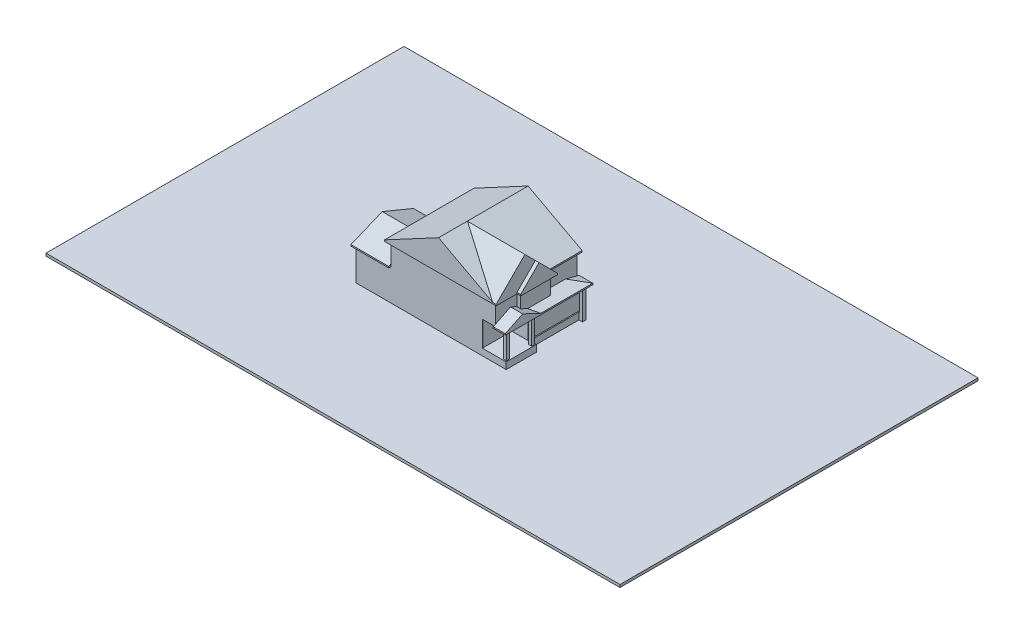
SolidWorks part; units mm, degrees
ref_plane "Front Plane" through (0, 0, 0) normal (0, 0, 1) x (1, 0, 0)
ref_plane "Top Plane" through (0, 0, 0) normal (0, 1, 0) x (1, 0, 0)
ref_plane "Right Plane" through (0, 0, 0) normal (1, 0, 0) x (0, 0, -1)
sketch "Sketch1" plane through (0, 0, 0) normal (0, 1, 0) x (1, 0, 0)
  line L0 (0, 0) -> (17208.5, 0)
  line L1 (0, 0) -> (0, 9448.8) construction
  line L2 (0, 0) -> (0, 6604)
  line L3 (0, 6604) -> (3048, 6604)
  line L4 (3048, 6604) -> (3048, 9448.8)
  line L5 (0, 9448.8) -> (17208.5, 9448.8) construction
  line L6 (3048, 9448.8) -> (16446.5, 9448.8)
  line L7 (16446.5, 9448.8) -> (16446.5, 0) construction
  line L8 (17208.5, 0) -> (17208.5, 3454.4)
  line L9 (17208.5, 9448.8) -> (17208.5, 0) construction
  line L10 (17208.5, 3454.4) -> (16446.5, 3454.4)
  line L11 (16446.5, 3454.4) -> (16446.5, 9093.2)
  line L12 (16446.5, 9093.2) -> (16852.9, 9093.2)
  line L13 (16852.9, 9093.2) -> (16852.9, 9448.8)
  line L14 (16852.9, 9448.8) -> (16446.5, 9448.8)
  line L15 (16852.9, 9448.8) -> (16852.9, 0) construction
extrude "Boss-Extrude1" add sketch "Sketch1" along normal blind 2603.5
ref_plane "Plane2" through (0, 2603.5, 0) normal (0, 1, 0) x (1, 0, 0)
sketch "Sketch2" plane through (0, 2603.5, 0) normal (0, 1, 0) x (1, 0, 0)
  line L11 (0, 0) -> (120.65, 0) construction
  line L12 (120.65, 127) -> (120.65, 6477)
  line L13 (120.65, 127) -> (14484.35, 127)
  line L14 (14484.35, 127) -> (14484.35, 3365.5)
  line L15 (14484.35, 3365.5) -> (16325.85, 3365.5)
  line L16 (120.65, 6477) -> (3168.65, 6477)
  line L17 (3168.65, 6477) -> (3168.65, 9328.15)
  line L18 (3168.65, 9328.15) -> (16325.85, 9328.15)
  line L19 (16325.85, 9328.15) -> (16325.85, 3365.5)
  line L20 (120.65, 127) -> (16325.85, 127) construction
  line L21 (0, 0) -> (17208.5, 0) construction
  line L22 (120.65, 0) -> (120.65, 127) construction
extrude "Boss-Extrude2" add sketch "Sketch2" along normal blind 3022.6
ref_plane "Plane3" through (0, 5626.1, 0) normal (0, 1, 0) x (1, 0, 0)
sketch "Sketch3" plane through (0, 5626.1, 0) normal (0, 1, 0) x (1, 0, 0)
  line L0 (16427.45, 9490.075) -> (4038.6, 9490.075) construction
  line L5 (4038.6, 9490.075) -> (15824.2, 9490.075)
  line L22 (4038.6, 9490.075) -> (4038.6, 53.975)
  line L23 (4038.6, 53.975) -> (16427.45, 53.975) construction
  line L24 (4038.6, 53.975) -> (16002, 53.975)
  line L25 (16427.45, 53.975) -> (16427.45, 9490.075) construction
  line L26 (16002, 53.975) -> (16002, 2435.225)
  line L27 (16002, 2435.225) -> (16427.45, 2435.225)
  line L28 (16427.45, 2435.225) -> (16427.45, 5832.475)
  line L29 (16427.45, 5832.475) -> (15824.2, 5832.475)
  line L30 (15824.2, 9490.075) -> (15824.2, 5832.475)
  point P6 (4038.6, 53.975)
extrude "Boss-Extrude3" add sketch "Sketch3" along normal blind 2463.8
ref_plane "Plane4" through (0, 1841.5, 0) normal (0, 1, 0) x (1, 0, 0)
sketch "Sketch4" plane through (0, 1841.5, 0) normal (0, 1, 0) x (1, 0, 0)
  line L10 (-20675.5654, 26188.1127) -> (45021.895, 26188.1127)
  line L11 (-20675.5654, 26188.1127) -> (-20675.5654, -14791.7177)
  line L12 (-20675.5654, -14791.7177) -> (45021.895, -14791.7177)
  line L13 (45021.895, 26188.1127) -> (45021.895, -14791.7177)
  line L14 (-20675.5654, 26188.1127) -> (45021.895, -14791.7177) construction
  line L15 (-20675.5654, -14791.7177) -> (45021.895, 26188.1127) construction
  point P0 (12173.1648, 5698.1975)
extrude "Boss-Extrude4" add sketch "Sketch4" against normal blind 304.8
sketch "Sketch5" plane through (0, 1536.7, 0) normal (0, -1, 0) x (1, 0, 0)
  line L1 (-2558.0149, -11208.2939) -> (19337.0017, -11208.2939)
  line L2 (-2558.0149, -11208.2939) -> (-2558.0149, 1114.2664)
  line L3 (-2558.0149, 1114.2664) -> (19337.0017, 1114.2664)
  line L4 (19337.0017, -11208.2939) -> (19337.0017, 1114.2664)
extrude "Cut-Extrude1" cut sketch "Sketch5" along normal blind 1905
ref_plane "Plane5" through (0, 8089.9, 0) normal (0, 1, 0) x (1, 0, 0)
ref_plane "Plane6" through (-285.75, 0, 0) normal (-1, 0, 0) x (0, 0, 1)
sketch "Sketch6" plane through (-285.75, 0, 0) normal (-1, 0, 0) x (0, 0, 1)
  line L0 (-127, 5626.1) -> (-6477, 5626.1)
  line L1 (-6477, 5626.1) -> (-6883.4, 5626.1)
  line L2 (2154.8725, 5626.1) -> (-2154.8725, 5626.1) construction
  line L3 (-127, 5626.1) -> (279.4, 5626.1)
  line L4 (-6883.4, 5626.1) -> (-3302, 7109.5645)
  line L5 (279.4, 5626.1) -> (-3302, 7109.5645)
extrude "Boss-Extrude5" add sketch "Sketch6" against normal up to surface (4324.35 mm away) up to face at (4038.6, 6447.3667, -4757.2083)
ref_plane "Plane8" through (0, 0, -9734.55) normal (0, 0, -1) x (-1, 0, 0)
sketch "Sketch8" plane through (0, 0, -9734.55) normal (0, 0, -1) x (-1, 0, 0)
  line L0 (-4038.6, 5626.1) -> (-3168.65, 5626.1)
  line L1 (-3168.65, 5626.1) -> (-2762.25, 5626.1)
  line L2 (-3168.65, 5626.1) -> (-120.65, 5626.1) construction
  line L3 (-2762.25, 5626.1) -> (-4038.6, 6154.7815)
  line L4 (-4038.6, 5626.1) -> (-4038.6, 6154.7815)
  line L5 (-4038.6, 7109.5645) -> (-4038.6, 5626.1) construction
extrude "Boss-Extrude6" add sketch "Sketch8" against normal up to surface (2851.15 mm away)
ref_plane "Plane9" through (2762.25, 0, 0) normal (-1, 0, 0) x (0, 0, 1)
sketch "Sketch9" plane through (2762.25, 0, 0) normal (-1, 0, 0) x (0, 0, 1)
  line L0 (-9734.55, 5626.1) -> (-8458.2, 6154.7815)
  line L1 (-9734.55, 5626.1) -> (-9734.55, 6154.7815)
  line L2 (-9734.55, 6154.7815) -> (-8458.2, 6154.7815)
extrude "Cut-Extrude2" cut sketch "Sketch9" against normal up to surface (1276.35 mm away) up to face at (4038.6, 6893.8526, -4666.1917)
ref_plane "Plane10" through (0, 0, -9896.475) normal (0, 0, -1) x (-1, 0, 0)
sketch "Sketch10" plane through (0, 0, -9896.475) normal (0, 0, -1) x (-1, 0, 0)
  line L0 (-4038.6, 8089.9) -> (-15824.2, 8089.9)
  line L1 (-15824.2, 8089.9) -> (-16230.6, 8089.9)
  line L2 (-4038.6, 8089.9) -> (-3632.2, 8089.9)
  line L3 (-3632.2, 8089.9) -> (-9931.4, 11456.8925)
  line L4 (-16230.6, 8089.9) -> (-9931.4, 11456.8925)
extrude "Boss-Extrude7" add sketch "Sketch10" against normal up to surface (9842.5 mm away) up to face at (8823.96, 6639.2377, -53.975)
sketch "Sketch11" plane through (0, 0, -53.975) normal (0, 0, 1) x (1, 0, 0)
  line L0 (3632.2, 8089.9) -> (9931.4, 11456.8925)
  line L1 (9931.4, 11456.8925) -> (16230.6, 8089.9)
  line L2 (16230.6, 8089.9) -> (3632.2, 8089.9)
extrude "Boss-Extrude8" add sketch "Sketch11" along normal blind 406.4
sketch "Sketch12" plane through (0, 0, 352.425) normal (0, 0, 1) x (1, 0, 0)
  line L0 (16002, 8089.9) -> (16230.6, 8089.9)
  line L1 (16230.6, 8089.9) -> (9931.4, 11456.8925)
  line L2 (16002, 8089.9) -> (9817.1, 11395.7979)
  line L3 (9931.4, 11456.8925) -> (9817.1, 11395.7979)
  line L4 (9931.4, 11456.8925) -> (3632.2, 8089.9) construction
extrude "Cut-Extrude3" cut sketch "Sketch12" against normal blind 11303
ref_plane "Plane11" through (16833.85, 0, 0) normal (1, 0, 0) x (0, 0, -1)
sketch "Sketch13" plane through (16833.85, 0, 0) normal (1, 0, 0) x (0, 0, -1)
  line L0 (5832.475, 8089.9) -> (2435.225, 8089.9)
  line L1 (2435.225, 8089.9) -> (2028.825, 8089.9)
  line L2 (53.975, 8089.9) -> (2435.225, 8089.9) construction
  line L3 (5832.475, 8089.9) -> (6238.875, 8089.9)
  line L4 (5832.475, 8089.9) -> (9490.075, 8089.9) construction
  line L5 (6238.875, 8089.9) -> (4133.85, 10194.925)
  line L6 (2028.825, 8089.9) -> (4133.85, 10194.925)
extrude "Boss-Extrude9" add sketch "Sketch13" against normal up to surface (831.85 mm away)
ref_plane "Plane12" through (16408.4, 0, 0) normal (1, 0, 0) x (0, 0, -1)
sketch "Sketch14" plane through (16408.4, 0, 0) normal (1, 0, 0) x (0, 0, -1)
  line L0 (-352.425, 8089.9) -> (2943.225, 11385.55)
  line L1 (4133.85, 10194.925) -> (2943.225, 11385.55)
  line L2 (-352.425, 8089.9) -> (2028.825, 8089.9)
  line L3 (2028.825, 8089.9) -> (4133.85, 10194.925)
extrude "Boss-Extrude10" add sketch "Sketch14" against normal up to surface (6572.1275 mm away)
sketch "Sketch15" plane through (0, 2603.5, 0) normal (0, 1, 0) x (1, 0, 0)
  line L0 (16852.9, 9093.2) -> (16446.5, 9093.2) construction
  line L1 (16852.9, 9448.8) -> (16497.3, 9448.8)
  line L2 (16852.9, 9448.8) -> (16852.9, 9093.2)
  line L3 (16852.9, 9093.2) -> (16497.3, 9093.2)
  line L4 (16497.3, 9448.8) -> (16497.3, 9093.2)
  line L5 (17208.5, 3454.4) -> (17106.9, 3454.4) construction
  line L6 (17208.5, 3454.4) -> (16446.5, 3454.4) construction
  line L7 (17106.9, 3454.4) -> (17106.9, 0) construction
  line L8 (17208.5, 0) -> (0, 0) construction
  line L9 (14599.9775, 126.9667) -> (17106.9, 126.9667) construction
  line L10 (14484.2237, 3365.4116) -> (17106.9, 3365.4116) construction
  line L11 (17106.9, 3009.8116) -> (16751.3, 3009.8116)
  line L12 (17106.9, 3365.4116) -> (16778.8236, 3365.4116)
  line L13 (17106.9, 3365.4116) -> (17106.9, 3009.8116)
  line L16 (17106.9, 126.9667) -> (16751.3, 126.9667)
  line L17 (17106.9, 126.9667) -> (17106.9, 482.5667)
  line L18 (17106.9, 482.5667) -> (16751.3, 482.5667)
  line L19 (16751.3, 126.9667) -> (16751.3, 482.5667)
  line L20 (16751.3, 3009.8116) -> (16751.3, 3365.4116)
  line L21 (16751.3, 3365.4116) -> (16778.8236, 3365.4116)
extrude "Boss-Extrude11" add sketch "Sketch15" along normal blind 3022.6
ref_plane "Plane13" through (0, 0, -9728.2) normal (0, 0, -1) x (-1, 0, 0)
sketch "Sketch16" plane through (0, 0, -9728.2) normal (0, 0, -1) x (-1, 0, 0)
  line L0 (-15824.2, 5626.1) -> (-17106.9, 5626.1)
  line L1 (-17106.9, 5626.1) -> (-17386.3, 5626.1)
  line L2 (-17386.3, 5626.1) -> (-15824.2, 6044.6634)
  line L3 (-15824.2, 5626.1) -> (-15824.2, 6044.6634)
extrude "Boss-Extrude12" add sketch "Sketch16" against normal blind 7362.952
ref_plane "Plane14" through (17132.3, 0, 0) normal (1, 0, 0) x (0, 0, -1)
sketch "Sketch17" plane through (17132.3, 0, 0) normal (1, 0, 0) x (0, 0, -1)
  line L0 (9734.55, 5626.1) -> (8172.45, 6044.6634)
  line L1 (9734.55, 5626.1) -> (9728.2, 6044.6634)
  line L2 (9728.2, 6044.6634) -> (8172.45, 6044.6634)
extrude "Cut-Extrude4" cut sketch "Sketch17" against normal up to surface (1308.1 mm away) and the other way blind 304.8 up to face at (15824.2, 7067.2817, -7661.275)
sketch "Sketch18" plane through (17132.3, 0, 0) normal (1, 0, 0) x (0, 0, -1)
  line L0 (-279.4, 5626.1) -> (1704.3334, 6604.369)
  line L1 (-279.4, 5626.1) -> (126.9667, 5626.1)
  line L2 (126.9667, 5626.1) -> (3365.4116, 5626.1)
  line L3 (3365.4116, 5626.1) -> (3771.8116, 5626.1)
  line L4 (2365.248, 5626.1) -> (9728.2, 5626.1) construction
  line L5 (3771.8116, 5626.1) -> (1704.3334, 6604.369)
extrude "Boss-Extrude13" add sketch "Sketch18" against normal up to surface and the other way blind 254 up to face at (16002, 6571.0074, -1618.1493)
sketch "Sketch19" plane through (0, 2603.5, 0) normal (0, 1, 0) x (1, 0, 0)
  line L1 (0, 0) -> (14484.5023, 0)
  line L2 (0, 0) -> (0, 133.0525)
  line L3 (0, 133.0525) -> (14484.5023, 133.0525)
  line L4 (14484.5023, 0) -> (14484.5023, 133.0525)
extrude "Boss-Extrude14" add sketch "Sketch19" along normal blind 3022.6
sketch "Sketch20" plane through (0, 5626.1, 0) normal (0, 1, 0) x (1, 0, 0)
  line L0 (17208.5, 0) -> (0, 0) construction
  line L1 (4038.6, 0) -> (14484.5023, 0)
  line L2 (4038.6, 0) -> (4038.6, 57.769)
  line L3 (4038.6, 57.769) -> (14484.5023, 57.769)
  line L4 (14484.5023, 0) -> (14484.5023, 57.769)
  line L5 (4038.6, 0) -> (14484.5023, 0) construction
  line L6 (14484.5023, 0) -> (14484.5023, 133.0525) construction
extrude "Boss-Extrude15" add sketch "Sketch20" along normal blind 2601.214
sketch "Sketch22" plane through (14484.5023, 0, 0) normal (1, 0, 0) x (0, 0, -1)
  line L1 (53.975, 5626.1) -> (0, 5626.1)
  line L2 (53.975, 5626.1) -> (53.975, 8089.9)
  line L3 (53.975, 8089.9) -> (0, 8089.9)
  line L4 (0, 5626.1) -> (0, 8089.9)
extrude "Boss-Extrude17" add sketch "Sketch22" along normal up to surface (1517.4977 mm away) up to face at (16002, 6966.6409, -1336.5467)
sketch "Sketch23" plane through (0, 2603.5, 0) normal (0, 1, 0) x (1, 0, 0)
  line L0 (0, 6604) -> (0, 133.0525)
  line L1 (120.65, 133.0525) -> (0, 133.0525)
  line L2 (120.65, 133.0525) -> (120.65, 6477)
  line L7 (3048, 6604) -> (0, 6604)
  line L9 (3048, 9448.8) -> (3168.65, 9448.8)
  line L10 (3048, 9448.8) -> (3048, 6604)
  line L12 (3168.65, 9328.15) -> (3168.65, 6477)
  line L13 (3168.65, 6477) -> (120.65, 6477)
  line L14 (3168.65, 9448.8) -> (16497.3, 9448.8)
  line L15 (16497.3, 9448.8) -> (16497.3, 9328.15)
  line L16 (16497.3, 9448.8) -> (16497.3, 9093.2) construction
  line L17 (16497.3, 9328.15) -> (3168.65, 9328.15)
extrude "Boss-Extrude18" add sketch "Sketch23" along normal blind 3022.6
sketch "Sketch24" plane through (0, 5626.1, 0) normal (0, -1, 0) x (1, 0, 0)
  line L1 (16852.9, -9448.8) -> (4038.6, -9448.8)
  line L2 (16852.9, -9448.8) -> (16852.9, -9490.075)
  line L3 (16852.9, -9490.075) -> (4038.6, -9490.075)
  line L5 (3048, -9448.8) -> (4038.6, -9448.8)
  line L6 (3048, -9448.8) -> (3048, -9490.075)
  line L7 (3048, -9490.075) -> (4038.6, -9490.075)
extrude "Boss-Extrude19" add sketch "Sketch24" along normal up to surface (3784.6 mm away) up to face at (12173.1648, 1841.5, -5698.1975)
sketch "Sketch25" plane through (0, 8089.9, 0) normal (0, -1, 0) x (1, 0, 0)
  line L45 (4140.2, -155.575) -> (4140.2, -9388.475)
  line L46 (4140.2, -9388.475) -> (15494, -9388.475)
  line L47 (15494, -9388.475) -> (15494, -5730.875)
  line L48 (15494, -5730.875) -> (16325.85, -5730.875)
  line L49 (16325.85, -5730.875) -> (16325.85, -2536.825)
  line L50 (16325.85, -2536.825) -> (15900.4, -2536.825)
  line L51 (15900.4, -2536.825) -> (15900.4, -155.575)
  line L52 (15900.4, -155.575) -> (15900.4, -155.575)
  line L53 (15900.4, -155.575) -> (4140.2, -155.575)
  line L54 (3632.2, 352.425) -> (3632.2, -9896.475)
  line L55 (16408.4, 352.425) -> (16002, 352.425)
  line L56 (16002, 352.425) -> (3632.2, 352.425)
  line L57 (16408.4, -2028.825) -> (16408.4, 352.425)
  line L58 (16833.85, -2028.825) -> (16408.4, -2028.825)
  line L59 (16833.85, -6238.875) -> (16833.85, -2028.825)
  line L60 (16002, -6238.875) -> (16833.85, -6238.875)
  line L61 (16002, -9896.475) -> (16002, -6238.875)
  line L62 (3632.2, -9896.475) -> (16002, -9896.475)
  line L63 (3632.2, 352.425) -> (3632.2, -9896.475)
  line L64 (16408.4, 352.425) -> (16002, 352.425)
  line L65 (16002, 352.425) -> (3632.2, 352.425)
  line L66 (16408.4, -2028.825) -> (16408.4, 352.425)
  line L67 (16833.85, -2028.825) -> (16408.4, -2028.825)
  line L68 (16833.85, -6238.875) -> (16833.85, -2028.825)
  line L69 (16002, -6238.875) -> (16833.85, -6238.875)
  line L70 (16002, -9896.475) -> (16002, -6238.875)
  line L71 (3632.2, -9896.475) -> (16002, -9896.475)
  dimension "D1" = 0
  dimension "D2" = 508
extrude "Boss-Extrude20" add sketch "Sketch25" along normal blind 152.4
sketch "Sketch26" plane through (0, 5626.1, 0) normal (0, -1, 0) x (1, 0, 0)
  line L120 (3530.6, -508) -> (3530.6, -228.6)
  line L121 (3530.6, -228.6) -> (222.25, -228.6)
  line L122 (222.25, -228.6) -> (222.25, -6375.4)
  line L123 (222.25, -6375.4) -> (3270.25, -6375.4)
  line L124 (3270.25, -6375.4) -> (3270.25, -9226.55)
  line L125 (3270.25, -9226.55) -> (3530.6, -9226.55)
  line L126 (3530.6, -9226.55) -> (3530.6, -8982.075)
  line L127 (3530.6, -8982.075) -> (16332.2, -8982.075)
  line L128 (16332.2, -8982.075) -> (16332.2, -9220.2)
  line L129 (16332.2, -9220.2) -> (16878.3, -9220.2)
  line L130 (16878.3, -9220.2) -> (16878.3, -3771.8116)
  line L131 (16878.3, -3771.8116) -> (16878.3, -228.6)
  line L132 (16878.3, -228.6) -> (16510, -228.6)
  line L133 (16510, -228.6) -> (16510, -508)
  line L134 (16510, -508) -> (3530.6, -508)
  line L135 (4038.6, 0) -> (4038.6, 279.4)
  line L136 (4038.6, 279.4) -> (-285.75, 279.4)
  line L137 (-285.75, 279.4) -> (-285.75, -6883.4)
  line L138 (-285.75, -6883.4) -> (2762.25, -6883.4)
  line L139 (2762.25, -6883.4) -> (2762.25, -9734.55)
  line L140 (2762.25, -9734.55) -> (4038.6, -9734.55)
  line L141 (4038.6, -9734.55) -> (4038.6, -9490.075)
  line L142 (4038.6, -9490.075) -> (15824.2, -9490.075)
  line L143 (15824.2, -9490.075) -> (15824.2, -9728.2)
  line L144 (15824.2, -9728.2) -> (17386.3, -9728.2)
  line L145 (17386.3, -9728.2) -> (17386.3, -3771.8116)
  line L146 (17386.3, -3771.8116) -> (17386.3, 279.4)
  line L147 (17386.3, 279.4) -> (16002, 279.4)
  line L148 (16002, 279.4) -> (16002, 0)
  line L149 (16002, 0) -> (4038.6, 0)
  line L150 (4038.6, 0) -> (4038.6, 279.4)
  line L151 (4038.6, 279.4) -> (-285.75, 279.4)
  line L152 (-285.75, 279.4) -> (-285.75, -6883.4)
  line L153 (-285.75, -6883.4) -> (2762.25, -6883.4)
  line L154 (2762.25, -6883.4) -> (2762.25, -9734.55)
  line L155 (2762.25, -9734.55) -> (4038.6, -9734.55)
  line L156 (4038.6, -9734.55) -> (4038.6, -9490.075)
  line L157 (4038.6, -9490.075) -> (15824.2, -9490.075)
  line L158 (15824.2, -9490.075) -> (15824.2, -9728.2)
  line L159 (15824.2, -9728.2) -> (17386.3, -9728.2)
  line L160 (17386.3, -9728.2) -> (17386.3, -3771.8116)
  line L161 (17386.3, -3771.8116) -> (17386.3, 279.4)
  line L162 (17386.3, 279.4) -> (16002, 279.4)
  line L163 (16002, 279.4) -> (16002, 0)
  line L164 (16002, 0) -> (4038.6, 0)
  dimension "D1" = 0
  dimension "D2" = 508
extrude "Boss-Extrude21" add sketch "Sketch26" along normal blind 152.4
sketch "Sketch27" plane through (0, 0, -9328.15) normal (0, 0, 1) x (1, 0, 0)
  line L0 (16497.3, 5473.7) -> (16497.3, 2603.5) construction
  line L1 (16325.85, 2603.5) -> (16497.3, 2603.5)
  line L2 (16325.85, 2603.5) -> (16325.85, 5473.7)
  line L3 (16325.85, 5473.7) -> (16497.3, 5473.7)
  line L4 (16497.3, 2603.5) -> (16497.3, 5473.7)
extrude "Cut-Extrude5" cut sketch "Sketch27" against normal blind 405.13
sketch "Truss Sketch 1" plane through (-2556.1241, 4782.1719, 0) normal (-0.4714, 0.8819, 0) x (0.8819, 0.4714, 0)
  line L0 (14029.8512, -352.425) -> (14029.8512, -314.325) construction
  line L1 (14029.8512, 9896.475) -> (14029.8512, -352.425) construction
  line L2 (14029.8512, -314.325) -> (7016.8669, -314.325) construction
  line L3 (7016.8669, -352.425) -> (7016.8669, 9896.475) construction
  line L4 (7016.8669, -314.325) -> (7016.8669, -352.425) construction
  line L5 (6945.026, -352.425) -> (7016.8669, -352.425) construction
  line L6 (7016.8669, -352.425) -> (14029.8512, -352.425) construction
  line L7 (14029.8512, 257.175) -> (14029.8512, 295.275) construction
  line L8 (14029.8512, 295.275) -> (7016.8669, 295.275) construction
  line L9 (7016.8669, 295.275) -> (7016.8669, 257.175) construction
  line L10 (7016.8669, 257.175) -> (14029.8512, 257.175) construction
  line L11 (14029.8512, 866.775) -> (14029.8512, 904.875) construction
  line L12 (14029.8512, 904.875) -> (7016.8669, 904.875) construction
  line L13 (7016.8669, 904.875) -> (7016.8669, 866.775) construction
  line L14 (7016.8669, 866.775) -> (14029.8512, 866.775) construction
  line L15 (14029.8512, 1476.375) -> (14029.8512, 1514.475) construction
  line L16 (14029.8512, 1514.475) -> (7016.8669, 1514.475) construction
  line L17 (7016.8669, 1514.475) -> (7016.8669, 1476.375) construction
  line L18 (7016.8669, 1476.375) -> (14029.8512, 1476.375) construction
  line L19 (14029.8512, 2085.975) -> (14029.8512, 2124.075) construction
  line L20 (14029.8512, 2124.075) -> (7016.8669, 2124.075) construction
  line L21 (7016.8669, 2124.075) -> (7016.8669, 2085.975) construction
  line L22 (7016.8669, 2085.975) -> (14029.8512, 2085.975) construction
  line L23 (14029.8512, 2695.575) -> (14029.8512, 2733.675) construction
  line L24 (14029.8512, 2733.675) -> (7016.8669, 2733.675) construction
  line L25 (7016.8669, 2733.675) -> (7016.8669, 2695.575) construction
  line L26 (7016.8669, 2695.575) -> (14029.8512, 2695.575) construction
  line L27 (14029.8512, 3305.175) -> (14029.8512, 3343.275) construction
  line L28 (14029.8512, 3343.275) -> (7016.8669, 3343.275) construction
  line L29 (7016.8669, 3343.275) -> (7016.8669, 3305.175) construction
  line L30 (7016.8669, 3305.175) -> (14029.8512, 3305.175) construction
  line L31 (14029.8512, 3914.775) -> (14029.8512, 3952.875) construction
  line L32 (14029.8512, 3952.875) -> (7016.8669, 3952.875) construction
  line L33 (7016.8669, 3952.875) -> (7016.8669, 3914.775) construction
  line L34 (7016.8669, 3914.775) -> (14029.8512, 3914.775) construction
  line L35 (14029.8512, 4524.375) -> (14029.8512, 4562.475) construction
  line L36 (14029.8512, 4562.475) -> (7016.8669, 4562.475) construction
  line L37 (7016.8669, 4562.475) -> (7016.8669, 4524.375) construction
  line L38 (7016.8669, 4524.375) -> (14029.8512, 4524.375) construction
  line L39 (14029.8512, 5133.975) -> (14029.8512, 5172.075) construction
  line L40 (14029.8512, 5172.075) -> (7016.8669, 5172.075) construction
  line L41 (7016.8669, 5172.075) -> (7016.8669, 5133.975) construction
  line L42 (7016.8669, 5133.975) -> (14029.8512, 5133.975) construction
  line L43 (14029.8512, 5743.575) -> (14029.8512, 5781.675) construction
  line L44 (14029.8512, 5781.675) -> (7016.8669, 5781.675) construction
  line L45 (7016.8669, 5781.675) -> (7016.8669, 5743.575) construction
  line L46 (7016.8669, 5743.575) -> (14029.8512, 5743.575) construction
  line L47 (14029.8512, 6353.175) -> (14029.8512, 6391.275) construction
  line L48 (14029.8512, 6391.275) -> (7016.8669, 6391.275) construction
  line L49 (7016.8669, 6391.275) -> (7016.8669, 6353.175) construction
  line L50 (7016.8669, 6353.175) -> (14029.8512, 6353.175) construction
  line L51 (14029.8512, 6962.775) -> (14029.8512, 7000.875) construction
  line L52 (14029.8512, 7000.875) -> (7016.8669, 7000.875) construction
  line L53 (7016.8669, 7000.875) -> (7016.8669, 6962.775) construction
  line L54 (7016.8669, 6962.775) -> (14029.8512, 6962.775) construction
  line L55 (14029.8512, 7572.375) -> (14029.8512, 7610.475) construction
  line L56 (14029.8512, 7610.475) -> (7016.8669, 7610.475) construction
  line L57 (7016.8669, 7610.475) -> (7016.8669, 7572.375) construction
  line L58 (7016.8669, 7572.375) -> (14029.8512, 7572.375) construction
  line L59 (14029.8512, 8181.975) -> (14029.8512, 8220.075) construction
  line L60 (14029.8512, 8220.075) -> (7016.8669, 8220.075) construction
  line L61 (7016.8669, 8220.075) -> (7016.8669, 8181.975) construction
  line L62 (7016.8669, 8181.975) -> (14029.8512, 8181.975) construction
  line L63 (14029.8512, 8791.575) -> (14029.8512, 8829.675) construction
  line L64 (14029.8512, 8829.675) -> (7016.8669, 8829.675) construction
  line L65 (7016.8669, 8829.675) -> (7016.8669, 8791.575) construction
  line L66 (7016.8669, 8791.575) -> (14029.8512, 8791.575) construction
  line L67 (14029.8512, 9401.175) -> (14029.8512, 9439.275) construction
  line L68 (14029.8512, 9439.275) -> (7016.8669, 9439.275) construction
  line L69 (7016.8669, 9439.275) -> (7016.8669, 9401.175) construction
  line L70 (7016.8669, 9401.175) -> (14029.8512, 9401.175) construction
  line L71 (14029.8512, 9896.475) -> (14029.8512, 9858.375) construction
  line L72 (14029.8512, 9858.375) -> (7016.8669, 9858.375) construction
  line L73 (7016.8669, 9858.375) -> (7016.8669, 9896.475) construction
  line L74 (7016.8669, 9896.475) -> (14029.8512, 9896.475) construction
  dimension "D1" = 17
sketch "Truss Sketch 2" plane through (0, 4900.9595, 2030.0439) normal (0, 0.9239, 0.3827) x (1, 0, 0)
  line L0 (4038.6, 5771.3627) -> (4038.6, 1894.8833) construction
  line L1 (4038.6, 1894.8833) -> (4000.5, 1894.8833) construction
  line L2 (4038.6, 1894.8833) -> (-285.75, 1894.8833) construction
  line L3 (4000.5, 1894.8833) -> (4000.5, 5771.3627) construction
  line L4 (4038.6, 5771.3627) -> (-285.75, 5771.3627) construction
  line L5 (4000.5, 5771.3627) -> (4038.6, 5771.3627) construction
  line L6 (-285.75, 1894.8833) -> (-285.75, 5771.3627) construction
  line L7 (-285.75, 5771.3627) -> (-247.65, 5771.3627) construction
  line L8 (-247.65, 5771.3627) -> (-247.65, 1894.8833) construction
  line L9 (-247.65, 1894.8833) -> (-285.75, 1894.8833) construction
  line L10 (323.85, 1894.8833) -> (323.85, 5771.3627) construction
  line L11 (323.85, 5771.3627) -> (361.95, 5771.3627) construction
  line L12 (361.95, 5771.3627) -> (361.95, 1894.8833) construction
  line L13 (361.95, 1894.8833) -> (323.85, 1894.8833) construction
  line L14 (933.45, 1894.8833) -> (933.45, 5771.3627) construction
  line L15 (933.45, 5771.3627) -> (971.55, 5771.3627) construction
  line L16 (971.55, 5771.3627) -> (971.55, 1894.8833) construction
  line L17 (971.55, 1894.8833) -> (933.45, 1894.8833) construction
  line L18 (1543.05, 1894.8833) -> (1543.05, 5771.3627) construction
  line L19 (1543.05, 5771.3627) -> (1581.15, 5771.3627) construction
  line L20 (1581.15, 5771.3627) -> (1581.15, 1894.8833) construction
  line L21 (1581.15, 1894.8833) -> (1543.05, 1894.8833) construction
  line L22 (2152.65, 1894.8833) -> (2152.65, 5771.3627) construction
  line L23 (2152.65, 5771.3627) -> (2190.75, 5771.3627) construction
  line L24 (2190.75, 5771.3627) -> (2190.75, 1894.8833) construction
  line L25 (2190.75, 1894.8833) -> (2152.65, 1894.8833) construction
  line L26 (2762.25, 1894.8833) -> (2762.25, 5771.3627) construction
  line L27 (2762.25, 5771.3627) -> (2800.35, 5771.3627) construction
  line L28 (2800.35, 5771.3627) -> (2800.35, 1894.8833) construction
  line L29 (2800.35, 1894.8833) -> (2762.25, 1894.8833) construction
  line L30 (3371.85, 1894.8833) -> (3371.85, 5771.3627) construction
  line L31 (3371.85, 5771.3627) -> (3409.95, 5771.3627) construction
  line L32 (3409.95, 5771.3627) -> (3409.95, 1894.8833) construction
  line L33 (3409.95, 1894.8833) -> (3371.85, 1894.8833) construction
  line L34 (3962.4, 5771.3627) -> (4000.5, 5771.3627) construction
  line L35 (3962.4, 1894.8833) -> (3962.4, 5771.3627) construction
  line L36 (4000.5, 5771.3627) -> (4000.5, 1894.8833) construction
  line L37 (4000.5, 1894.8833) -> (3962.4, 1894.8833) construction
  dimension "D1" = 7
  dimension "D2" = 2
sketch "Truss Sketch 3" plane through (0, 4221.1625, 4221.1625) normal (0, 0.7071, 0.7071) x (1, 0, 0)
  line L0 (16408.4, 10131.974) -> (16408.4, 5471.221) construction
  line L1 (16408.4, 5471.221) -> (16370.3, 5471.221) construction
  line L2 (16002, 5471.221) -> (16408.4, 5471.221) construction
  line L3 (16370.3, 5471.221) -> (16370.3, 10131.974) construction
  line L4 (9836.2725, 10131.974) -> (16408.4, 10131.974) construction
  line L5 (16370.3, 10131.974) -> (16408.4, 10131.974) construction
  line L6 (9836.2725, 10131.974) -> (16002, 5471.221) construction
  line L7 (15798.8, 10131.974) -> (15798.8, 5624.8225) construction
  line L8 (16408.4, 10131.974) -> (11455.4, 10131.974) construction
  line L9 (15760.7, 5653.6228) -> (15760.7, 10131.974) construction
  line L10 (15760.7, 10131.974) -> (15798.8, 10131.974) construction
  line L11 (15189.2, 10131.974) -> (15189.2, 6085.627) construction
  line L13 (15151.1, 6114.4273) -> (15151.1, 10131.974) construction
  line L14 (15151.1, 10131.974) -> (15189.2, 10131.974) construction
  line L15 (14579.6, 10131.974) -> (14579.6, 6546.4315) construction
  line L17 (14541.5, 6575.2318) -> (14541.5, 10131.974) construction
  line L18 (14541.5, 10131.974) -> (14579.6, 10131.974) construction
  line L19 (13970, 10131.974) -> (13970, 7007.236) construction
  line L20 (16408.4, 9115.974) -> (16408.4, 8099.974) construction
  line L21 (13931.9, 7036.0363) -> (13931.9, 10131.974) construction
  line L22 (13931.9, 10131.974) -> (13970, 10131.974) construction
  line L23 (13360.4, 10131.974) -> (13360.4, 7468.0406) construction
  line L25 (13322.3, 7496.8408) -> (13322.3, 10131.974) construction
  line L26 (13322.3, 10131.974) -> (13360.4, 10131.974) construction
  line L27 (12750.8, 10131.974) -> (12750.8, 7928.8451) construction
  line L29 (12712.7, 7957.6453) -> (12712.7, 10131.974) construction
  line L30 (12712.7, 10131.974) -> (12750.8, 10131.974) construction
  line L31 (12141.2, 10131.974) -> (12141.2, 8389.6496) construction
  line L33 (12103.1, 8418.4498) -> (12103.1, 10131.974) construction
  line L34 (12103.1, 10131.974) -> (12141.2, 10131.974) construction
  line L35 (11531.6, 10131.974) -> (11531.6, 8850.4541) construction
  line L37 (11493.5, 8879.2543) -> (11493.5, 10131.974) construction
  line L38 (11493.5, 10131.974) -> (11531.6, 10131.974) construction
  line L39 (10922, 10131.974) -> (10922, 9311.2586) construction
  line L41 (10883.9, 9340.0588) -> (10883.9, 10131.974) construction
  line L42 (10883.9, 10131.974) -> (10922, 10131.974) construction
  line L43 (10312.4, 10131.974) -> (10312.4, 9772.0631) construction
  line L45 (10274.3, 9800.8633) -> (10274.3, 10131.974) construction
  line L46 (10274.3, 10131.974) -> (10312.4, 10131.974) construction
  line L47 (15798.8, 5471.221) -> (15760.7, 5471.221) construction
  line L48 (15189.2, 5471.221) -> (15151.1, 5471.221) construction
  line L49 (14579.6, 5471.221) -> (14541.5, 5471.221) construction
  line L50 (13970, 5471.221) -> (13931.9, 5471.221) construction
  line L51 (13360.4, 5471.221) -> (13322.3, 5471.221) construction
  line L52 (12750.8, 5471.221) -> (12712.7, 5471.221) construction
  line L53 (12141.2, 5471.221) -> (12103.1, 5471.221) construction
  line L54 (11531.6, 5471.221) -> (11493.5, 5471.221) construction
  line L55 (10922, 5471.221) -> (10883.9, 5471.221) construction
  line L56 (10312.4, 5471.221) -> (10274.3, 5471.221) construction
  dimension "D1" = 11
sketch "Truss Sketch 4" plane through (6919.1356, 12944.7922, 0) normal (0.4714, 0.8819, 0) x (0.8819, -0.4714, 0)
  line L0 (3285.9673, 9896.475) -> (10298.9516, 9896.475) construction
  line L1 (10298.9516, 9896.475) -> (10298.9516, 9858.375) construction
  line L2 (10298.9516, 9896.475) -> (10298.9516, 6238.875) construction
  line L3 (10298.9516, 9858.375) -> (3285.9673, 9858.375) construction
  line L4 (3285.9673, 9858.375) -> (3285.9673, 9896.475) construction
  line L5 (10298.9516, 6238.875) -> (3307.7068, 2943.225) construction
  line L6 (3307.7068, 2943.225) -> (10298.9516, -352.425) construction
  line L7 (3285.9673, -352.425) -> (10298.9516, -352.425) construction
  line L8 (10298.9516, -352.425) -> (10298.9516, -314.325) construction
  line L9 (10298.9516, -314.325) -> (3285.9673, -314.325) construction
  line L10 (3285.9673, -314.325) -> (3285.9673, -352.425) construction
  line L11 (3285.9673, 257.175) -> (9005.7734, 257.175) construction
  line L13 (8924.9497, 295.275) -> (3285.9673, 295.275) construction
  line L14 (3285.9673, 295.275) -> (3285.9673, 257.175) construction
  line L15 (3285.9673, 866.775) -> (7712.5951, 866.775) construction
  line L17 (7631.7715, 904.875) -> (3285.9673, 904.875) construction
  line L18 (3285.9673, 904.875) -> (3285.9673, 866.775) construction
  line L19 (3285.9673, 1476.375) -> (6419.4169, 1476.375) construction
  line L21 (6338.5933, 1514.475) -> (3285.9673, 1514.475) construction
  line L22 (3285.9673, 1514.475) -> (3285.9673, 1476.375) construction
  line L23 (3285.9673, 2085.975) -> (5126.2387, 2085.975) construction
  line L25 (5045.415, 2124.075) -> (3285.9673, 2124.075) construction
  line L26 (3285.9673, 2124.075) -> (3285.9673, 2085.975) construction
  line L27 (3285.9673, 2695.575) -> (3833.0604, 2695.575) construction
  line L29 (3752.2368, 2733.675) -> (3285.9673, 2733.675) construction
  line L30 (3285.9673, 2733.675) -> (3285.9673, 2695.575) construction
  line L31 (3285.9673, 3305.175) -> (4075.5314, 3305.175) construction
  line L33 (4156.355, 3343.275) -> (3285.9673, 3343.275) construction
  line L34 (3285.9673, 3343.275) -> (3285.9673, 3305.175) construction
  line L35 (3285.9673, 3914.775) -> (5368.7096, 3914.775) construction
  line L37 (5449.5332, 3952.875) -> (3285.9673, 3952.875) construction
  line L38 (3285.9673, 3952.875) -> (3285.9673, 3914.775) construction
  line L39 (3285.9673, 4524.375) -> (6661.8878, 4524.375) construction
  line L41 (6742.7115, 4562.475) -> (3285.9673, 4562.475) construction
  line L42 (3285.9673, 4562.475) -> (3285.9673, 4524.375) construction
  line L43 (3285.9673, 5133.975) -> (7955.0661, 5133.975) construction
  line L45 (8035.8897, 5172.075) -> (3285.9673, 5172.075) construction
  line L46 (3285.9673, 5172.075) -> (3285.9673, 5133.975) construction
  line L47 (3285.9673, 5743.575) -> (9248.2443, 5743.575) construction
  line L49 (9329.0679, 5781.675) -> (3285.9673, 5781.675) construction
  line L50 (3285.9673, 5781.675) -> (3285.9673, 5743.575) construction
  line L51 (3285.9673, 6353.175) -> (10298.9516, 6353.175) construction
  line L52 (10298.9516, 6353.175) -> (10298.9516, 6391.275) construction
  line L53 (10298.9516, 6391.275) -> (3285.9673, 6391.275) construction
  line L54 (3285.9673, 6391.275) -> (3285.9673, 6353.175) construction
  line L55 (3285.9673, 6962.775) -> (10298.9516, 6962.775) construction
  line L56 (10298.9516, 6962.775) -> (10298.9516, 7000.875) construction
  line L57 (10298.9516, 7000.875) -> (3285.9673, 7000.875) construction
  line L58 (3285.9673, 7000.875) -> (3285.9673, 6962.775) construction
  line L59 (3285.9673, 7572.375) -> (10298.9516, 7572.375) construction
  line L60 (10298.9516, 7572.375) -> (10298.9516, 7610.475) construction
  line L61 (10298.9516, 7610.475) -> (3285.9673, 7610.475) construction
  line L62 (3285.9673, 7610.475) -> (3285.9673, 7572.375) construction
  line L63 (3285.9673, 8181.975) -> (10298.9516, 8181.975) construction
  line L64 (10298.9516, 8181.975) -> (10298.9516, 8220.075) construction
  line L65 (10298.9516, 8220.075) -> (3285.9673, 8220.075) construction
  line L66 (3285.9673, 8220.075) -> (3285.9673, 8181.975) construction
  line L67 (3285.9673, 8791.575) -> (10298.9516, 8791.575) construction
  line L68 (10298.9516, 8791.575) -> (10298.9516, 8829.675) construction
  line L69 (10298.9516, 8829.675) -> (3285.9673, 8829.675) construction
  line L70 (3285.9673, 8829.675) -> (3285.9673, 8791.575) construction
  line L71 (3285.9673, 9401.175) -> (10298.9516, 9401.175) construction
  line L72 (10298.9516, 9401.175) -> (10298.9516, 9439.275) construction
  line L73 (10298.9516, 9439.275) -> (3285.9673, 9439.275) construction
  line L74 (3285.9673, 9439.275) -> (3285.9673, 9401.175) construction
  line L75 (10298.9516, 257.175) -> (10298.9516, 295.275) construction
  line L76 (10298.9516, 866.775) -> (10298.9516, 904.875) construction
  line L77 (10298.9516, 1476.375) -> (10298.9516, 1514.475) construction
  line L78 (10298.9516, 2085.975) -> (10298.9516, 2124.075) construction
  line L79 (10298.9516, 2695.575) -> (10298.9516, 2733.675) construction
  line L80 (10298.9516, 3305.175) -> (10298.9516, 3343.275) construction
  line L81 (10298.9516, 3914.775) -> (10298.9516, 3952.875) construction
  line L82 (10298.9516, 4524.375) -> (10298.9516, 4562.475) construction
  line L83 (10298.9516, 5133.975) -> (10298.9516, 5172.075) construction
  line L84 (10298.9516, 5743.575) -> (10298.9516, 5781.675) construction
  dimension "D1" = 17
sketch "Truss Sketch 5" plane through (0, 7164.3875, -7164.3875) normal (0, 0.7071, -0.7071) x (1, 0, 0)
  line L0 (16408.4, -5969.6253) -> (16370.3, -5969.6253) construction
  line L1 (15798.8, -5969.6253) -> (15760.7, -5969.6253) construction
  line L2 (15760.7, -5969.6253) -> (15760.7, -1491.2741) construction
  line L3 (16833.85, -4285.8272) -> (16833.85, -1308.8723) construction
  line L4 (9836.2725, -5969.6253) -> (16408.4, -5969.6253) construction
  line L5 (16370.3, -5969.6253) -> (16370.3, -1308.8723) construction
  line L6 (16002, -1308.8723) -> (16833.85, -1308.8723) construction
  line L7 (16370.3, -1308.8723) -> (16408.4, -1308.8723) construction
  line L8 (16408.4, -1308.8723) -> (16408.4, -5969.6253) construction
  line L9 (9836.2725, -5969.6253) -> (16002, -1308.8723) construction
  line L10 (15798.8, -1462.4738) -> (15798.8, -5969.6253) construction
  line L11 (15189.2, -5969.6253) -> (15151.1, -5969.6253) construction
  line L12 (15151.1, -5969.6253) -> (15151.1, -1952.0786) construction
  line L13 (16833.85, -1308.8723) -> (16795.75, -1308.8723) construction
  line L14 (15189.2, -1923.2783) -> (15189.2, -5969.6253) construction
  line L15 (14579.6, -5969.6253) -> (14541.5, -5969.6253) construction
  line L16 (14541.5, -5969.6253) -> (14541.5, -2412.8831) construction
  line L17 (16795.75, -1308.8723) -> (16795.75, -4285.8272) construction
  line L18 (14579.6, -2384.0828) -> (14579.6, -5969.6253) construction
  line L19 (13970, -5969.6253) -> (13931.9, -5969.6253) construction
  line L20 (13931.9, -5969.6253) -> (13931.9, -2873.6876) construction
  line L21 (16408.4, -4285.8272) -> (16833.85, -4285.8272) construction
  line L22 (13970, -2844.8873) -> (13970, -5969.6253) construction
  line L23 (13360.4, -5969.6253) -> (13322.3, -5969.6253) construction
  line L24 (13322.3, -5969.6253) -> (13322.3, -3334.4921) construction
  line L25 (16795.75, -4285.8272) -> (16833.85, -4285.8272) construction
  line L26 (13360.4, -3305.6918) -> (13360.4, -5969.6253) construction
  line L27 (12750.8, -5969.6253) -> (12712.7, -5969.6253) construction
  line L28 (12712.7, -5969.6253) -> (12712.7, -3795.2966) construction
  line L30 (12750.8, -3766.4963) -> (12750.8, -5969.6253) construction
  line L31 (12141.2, -5969.6253) -> (12103.1, -5969.6253) construction
  line L32 (12103.1, -5969.6253) -> (12103.1, -4256.1011) construction
  line L34 (12141.2, -4227.3008) -> (12141.2, -5969.6253) construction
  line L35 (11531.6, -5969.6253) -> (11493.5, -5969.6253) construction
  line L36 (11493.5, -5969.6253) -> (11493.5, -4716.9056) construction
  line L38 (11531.6, -4688.1053) -> (11531.6, -5969.6253) construction
  line L39 (10922, -5969.6253) -> (10883.9, -5969.6253) construction
  line L40 (10883.9, -5969.6253) -> (10883.9, -5177.7101) construction
  line L42 (10922, -5148.9098) -> (10922, -5969.6253) construction
  line L43 (10312.4, -5969.6253) -> (10274.3, -5969.6253) construction
  line L44 (10274.3, -5969.6253) -> (10274.3, -5638.5146) construction
  line L46 (10312.4, -5609.7144) -> (10312.4, -5969.6253) construction
  line L47 (10274.3, -1308.8723) -> (10312.4, -1308.8723) construction
  line L48 (10883.9, -1308.8723) -> (10922, -1308.8723) construction
  line L49 (11493.5, -1308.8723) -> (11531.6, -1308.8723) construction
  line L50 (12103.1, -1308.8723) -> (12141.2, -1308.8723) construction
  line L51 (12712.7, -1308.8723) -> (12750.8, -1308.8723) construction
  line L52 (13322.3, -1308.8723) -> (13360.4, -1308.8723) construction
  line L53 (13931.9, -1308.8723) -> (13970, -1308.8723) construction
  line L54 (14541.5, -1308.8723) -> (14579.6, -1308.8723) construction
  line L55 (15151.1, -1308.8723) -> (15189.2, -1308.8723) construction
  line L56 (15760.7, -1308.8723) -> (15798.8, -1308.8723) construction
  dimension "D1" = 11
sketch "Truss Sketch 6" plane through (0, 7235.8261, -2997.1773) normal (0, 0.9239, -0.3827) x (1, 0, 0)
  line L0 (-285.75, 329.9377) -> (-247.65, 329.9377) construction
  line L1 (-247.65, 329.9377) -> (-247.65, 4206.4171) construction
  line L2 (2762.25, 4206.4171) -> (-285.75, 4206.4171) construction
  line L3 (-247.65, 4206.4171) -> (-285.75, 4206.4171) construction
  line L4 (-285.75, 4206.4171) -> (-285.75, 329.9377) construction
  line L5 (2762.25, 4206.4171) -> (4038.6, 2824.9058) construction
  line L6 (323.85, 329.9377) -> (361.95, 329.9377) construction
  line L7 (361.95, 329.9377) -> (361.95, 4206.4171) construction
  line L8 (361.95, 4206.4171) -> (323.85, 4206.4171) construction
  line L9 (323.85, 4206.4171) -> (323.85, 329.9377) construction
  line L10 (933.45, 329.9377) -> (971.55, 329.9377) construction
  line L11 (971.55, 329.9377) -> (971.55, 4206.4171) construction
  line L12 (971.55, 4206.4171) -> (933.45, 4206.4171) construction
  line L13 (933.45, 4206.4171) -> (933.45, 329.9377) construction
  line L14 (1543.05, 329.9377) -> (1581.15, 329.9377) construction
  line L15 (1581.15, 329.9377) -> (1581.15, 4206.4171) construction
  line L16 (1581.15, 4206.4171) -> (1543.05, 4206.4171) construction
  line L17 (1543.05, 4206.4171) -> (1543.05, 329.9377) construction
  line L18 (2152.65, 329.9377) -> (2190.75, 329.9377) construction
  line L19 (2190.75, 329.9377) -> (2190.75, 4206.4171) construction
  line L20 (2190.75, 4206.4171) -> (2152.65, 4206.4171) construction
  line L21 (2152.65, 4206.4171) -> (2152.65, 329.9377) construction
  line L22 (2762.25, 329.9377) -> (2800.35, 329.9377) construction
  line L23 (2800.35, 329.9377) -> (2800.35, 4165.178) construction
  line L24 (4038.6, 329.9377) -> (4000.5, 329.9377) construction
  line L25 (2762.25, 4206.4171) -> (2762.25, 329.9377) construction
  line L26 (3371.85, 329.9377) -> (3409.95, 329.9377) construction
  line L27 (3409.95, 329.9377) -> (3409.95, 3505.3517) construction
  line L28 (4000.5, 329.9377) -> (3962.4, 329.9377) construction
  line L29 (3371.85, 3546.5908) -> (3371.85, 329.9377) construction
  line L30 (3409.95, 4206.4171) -> (3371.85, 4206.4171) construction
  line L31 (2800.35, 4206.4171) -> (2762.25, 4206.4171) construction
  line L32 (3962.4, 329.9377) -> (3962.4, 2907.3841) construction
  line L33 (4038.6, 2824.9058) -> (4038.6, 329.9377) construction
  line L34 (4000.5, 329.9377) -> (4000.5, 2866.145) construction
  dimension "D1" = 7
